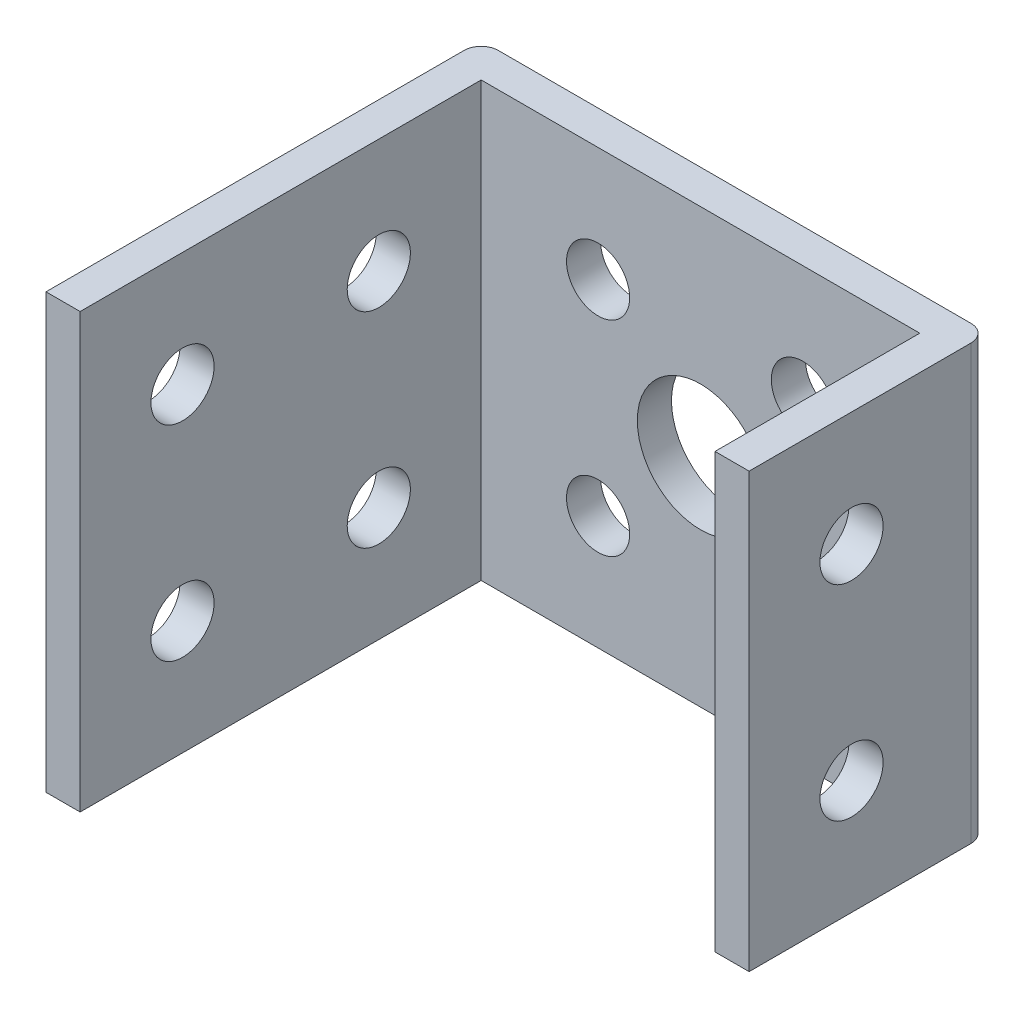
SolidWorks part; units mm, degrees
ref_plane "Front Plane" through (0, 0, 0) normal (0, 0, 1) x (1, 0, 0)
ref_plane "Top Plane" through (0, 0, 0) normal (0, 1, 0) x (1, 0, 0)
ref_plane "Right Plane" through (0, 0, 0) normal (1, 0, 0) x (0, 0, -1)
sketch "Sketch1" plane through (0, 0, 0) normal (0, 1, 0) x (1, 0, 0)
  line L0 (0, 0) -> (0, 31.75) construction
  line L1 (-14.85, 0) -> (14.85, 0)
  line L2 (14.85, 0) -> (14.85, -14)
  line L3 (14.85, -14) -> (12.85, -14)
  line L4 (12.85, -14) -> (12.85, -2)
  line L5 (12.85, -2) -> (-12.85, -2)
  line L6 (-12.85, -2) -> (-12.85, -14)
  line L7 (-12.85, -14) -> (-14.85, -14)
  line L8 (-14.85, -14) -> (-14.85, 0)
  dimension "D1" = 2
  dimension "D2" = 29.7
  dimension "D3" = 2
  dimension "D4" = 12
extrude "Boss-Extrude1" add sketch "Sketch1" along normal mid plane 25.4
sketch "Sketch2" plane through (-14.85, 0, 0) normal (-1, 0, 0) x (0, 0, 1)
  line L0 (0, 0) -> (21.026, 0) construction
  line L2 (0, 12.7) -> (0, -12.7) construction
  circle A0 centre (8, -6) radius 1.85
  circle A1 centre (8, 6) radius 1.85
  dimension "D1" = 3.7
  dimension "D2" = 12
  dimension "D3" = 8
extrude "Cut-Extrude1" cut sketch "Sketch2" against normal through all
sketch "Sketch3" plane through (0, 0, 0) normal (0, 0, -1) x (-1, 0, 0)
  circle A0 centre (0, 0) radius 3.7
  dimension "D1" = 7.4
extrude "Cut-Extrude2" cut sketch "Sketch3" against normal through all
sketch "Sketch4" plane through (0, 0, 2) normal (0, 0, 1) x (1, 0, 0)
  line L0 (0, 0) -> (0, 13.4152) construction
  line L1 (0, 0) -> (18.1171, 0) construction
  circle A0 centre (-6, 6) radius 1.85
  circle A1 centre (-6, -6) radius 1.85
  circle A2 centre (6, -6) radius 1.85
  circle A3 centre (6, 6) radius 1.85
  dimension "D3" = 3.7
  dimension "D1" = 12
  dimension "D2" = 12
extrude "Cut-Extrude3" cut sketch "Sketch4" against normal through all
sketch "Sketch5" plane through (-14.85, 0, 0) normal (1, 0, 0) x (0, 0, -1)
  line L0 (-8, 6) -> (-35.1094, 6) construction
  line L1 (-14, 12.7) -> (-25.5, 12.7)
  line L2 (-14, 12.7) -> (-14, -12.7)
  line L3 (-14, -12.7) -> (-25.5, -12.7)
  line L4 (-25.5, 12.7) -> (-25.5, -12.7)
  line L5 (-8, -6) -> (-35.1094, -6) construction
  circle A0 centre (-19.5, 6) radius 1.85
  circle A1 centre (-19.5, -6) radius 1.85
  dimension "D3" = 3.7
  dimension "D1" = 11.5
extrude "Boss-Extrude2" add sketch "Sketch5" along normal up to surface (2 mm away) up to face at (-12.85, 6, 9.85)
fillet "Fillet1" radius 1 2 edges at (14.85, 0, 0) (-14.85, 0, 0)
